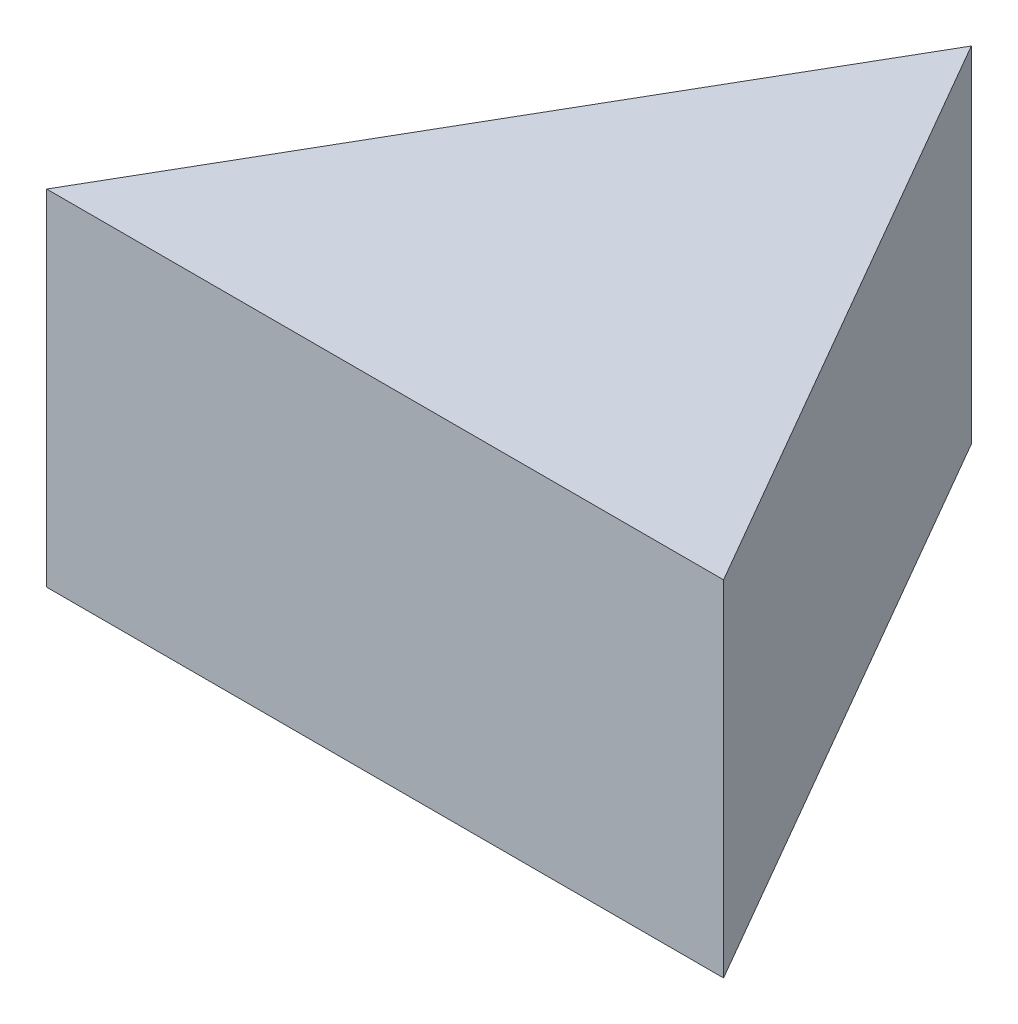
SolidWorks part; units mm, degrees
ref_plane "Front Plane" through (0, 0, 0) normal (0, 0, 1) x (1, 0, 0)
ref_plane "Top Plane" through (0, 0, 0) normal (0, 1, 0) x (1, 0, 0)
ref_plane "Right Plane" through (0, 0, 0) normal (1, 0, 0) x (0, 0, -1)
sketch "Sketch1" plane through (0, 0, 0) normal (0, 1, 0) x (1, 0, 0)
  line L0 (-7.4075, 12.0475) -> (-17.2224, -4.9525)
  line L1 (-7.4075, 12.0475) -> (2.4075, -4.9525)
  line L2 (-17.2224, -4.9525) -> (2.4075, -4.9525)
  dimension "D1" = 17
  dimension "D2" = 60
  dimension "D3" = 60
extrude "Boss-Extrude1" add sketch "Sketch1" along normal blind 10 contours L1 L2 L0
